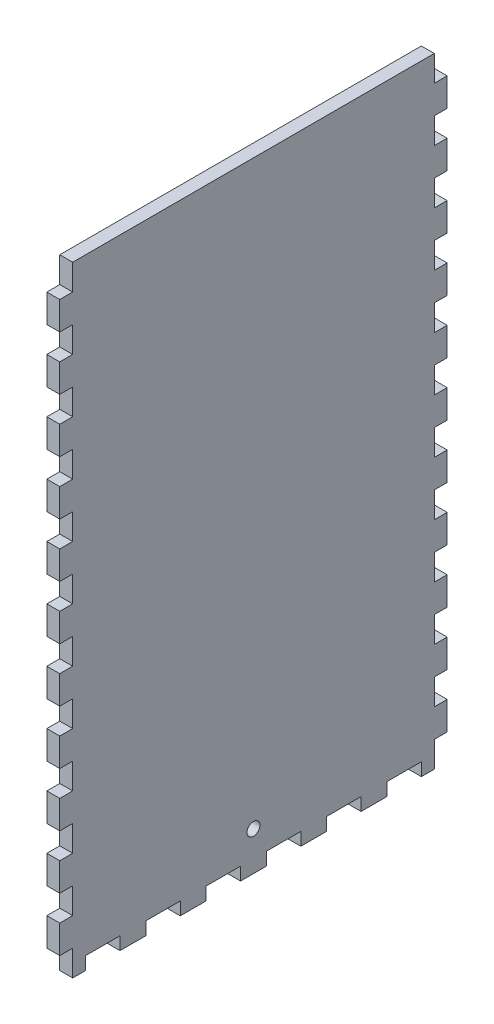
SolidWorks part; units mm, degrees
material "Acrylic (Medium-high impact)"
ref_plane "Front Plane" through (0, 0, 0) normal (0, 0, 1) x (1, 0, 0)
ref_plane "Top Plane" through (0, 0, 0) normal (0, 1, 0) x (1, 0, 0)
ref_plane "Right Plane" through (0, 0, 0) normal (1, 0, 0) x (0, 0, -1)
sketch "Sketch1" plane through (0, 0, 0) normal (0, 1, 0) x (1, 0, 0)
  line L1 (-254, 95.25) -> (254, 95.25)
  line L2 (-254, 95.25) -> (-254, -95.25)
  line L3 (-254, -95.25) -> (254, -95.25)
  line L4 (254, 95.25) -> (254, -95.25)
  point P4 (-254, 0)
  point P6 (0, 95.25)
  dimension "D1" = 190.5
  dimension "D2" = 508
extrude "Boss-Extrude1" add sketch "Sketch1" along normal blind 6.35
sketch "Sketch2" plane through (0, 6.35, 0) normal (0, 1, 0) x (1, 0, 0)
  line L0 (254, -95.25) -> (254, 95.25) construction
  line L1 (-254, 95.25) -> (254, 95.25)
  line L2 (-254, 95.25) -> (-254, -95.25)
  line L3 (-254, -95.25) -> (254, -95.25)
  line L4 (254, 95.25) -> (254, -95.25)
  line L5 (-254, -95.25) -> (254, -95.25) construction
  line L7 (-247.65, 88.9) -> (247.65, 88.9)
  line L8 (-247.65, 88.9) -> (-247.65, -88.9)
  line L9 (-247.65, -88.9) -> (247.65, -88.9)
  line L10 (247.65, 88.9) -> (247.65, -88.9)
  point P7 (-247.65, 0)
  point P14 (-254, 0)
  point P15 (0, -88.9)
  point P16 (0, -95.25)
  point P17 (247.65, 0)
  point P18 (254, 0)
  dimension "D1" = 6.35
  dimension "D2" = 6.35
extrude "Boss-Extrude2" add sketch "Sketch2" along normal blind 298.45
sketch "Sketch3" plane through (0, 0, 95.25) normal (0, 0, 1) x (1, 0, 0)
  line L0 (0, 304.8) -> (0, 0) construction
  line L1 (-254, 304.8) -> (254, 304.8) construction
  line L2 (-247.65, 6.35) -> (247.65, 6.35) construction
  line L4 (-3.302, 283.21) -> (-3.302, 6.35)
  line L5 (-3.302, 6.35) -> (3.302, 6.35)
  line L6 (3.302, 292.354) -> (3.302, 6.35)
  line L7 (3.302, 292.354) -> (-16.256, 292.354)
  line L9 (-5.842, 285.75) -> (-16.256, 285.75)
  line L10 (-16.256, 292.354) -> (-16.256, 285.75)
  line L11 (3.302, 101.6) -> (16.002, 101.6) construction
  line L12 (-254, 0) -> (254, 0) construction
  line L13 (12.827, 88.9) -> (12.827, 101.6) construction
  line L14 (9.652, 88.9) -> (16.002, 88.9)
  line L15 (9.652, 88.9) -> (9.652, 71.9667)
  line L16 (9.652, 71.9667) -> (16.002, 71.9667)
  line L17 (16.002, 88.9) -> (16.002, 71.9667)
  line L18 (9.652, 42.3333) -> (16.002, 42.3333)
  line L19 (9.652, 42.3333) -> (9.652, 59.2667)
  line L20 (9.652, 59.2667) -> (16.002, 59.2667)
  line L21 (16.002, 42.3333) -> (16.002, 59.2667)
  line L26 (9.652, 29.6333) -> (16.002, 29.6333)
  line L27 (9.652, 29.6333) -> (9.652, 12.7)
  line L28 (9.652, 12.7) -> (16.002, 12.7)
  line L29 (16.002, 29.6333) -> (16.002, 12.7)
  line L30 (12.827, 59.2667) -> (12.827, 71.9667) construction
  line L31 (12.827, 29.6333) -> (12.827, 42.3333) construction
  line L32 (12.827, 12.7) -> (12.827, 0) construction
  arc A0 (-3.302, 283.21) -> (-5.842, 285.75) centre (-5.842, 283.21) ccw
  point P5 (0, 6.35)
  dimension "D5" = 2.54
  dimension "D1" = 6.604
  dimension "D2" = 12.954
  dimension "D3" = 6.604
  dimension "D4" = 286.004
  dimension "D6" = 101.6
  dimension "D7" = 12.7
  dimension "D8" = 12.7
  dimension "D9" = 6.35
extrude "Cut-Extrude1" cut sketch "Sketch3" against normal blind 12.7
sketch "Sketch4" plane through (0, 0, -88.9) normal (0, 0, 1) x (1, 0, 0)
  line L0 (-254, 304.8) -> (254, 304.8) construction
  line L1 (-22.606, 304.8) -> (-16.256, 304.8)
  line L2 (-22.606, 304.8) -> (-22.606, 6.35)
  line L3 (-22.606, 6.35) -> (-16.256, 6.35)
  line L4 (-16.256, 304.8) -> (-16.256, 6.35)
  line L5 (6.477, 263.525) -> (6.477, 247.65) construction
  line L6 (-16.256, 292.354) -> (-16.256, 285.75) construction
  line L7 (3.302, 304.8) -> (9.652, 304.8)
  line L8 (3.302, 304.8) -> (3.302, 6.35)
  line L9 (3.302, 6.35) -> (9.652, 6.35)
  line L10 (9.652, 304.8) -> (9.652, 6.35)
  line L11 (247.65, 6.35) -> (-247.65, 6.35) construction
  line L12 (3.302, 6.35) -> (3.302, 292.354) construction
  line L13 (-16.256, 304.8) -> (-22.606, 304.8)
  line L14 (-16.256, 304.8) -> (-16.256, 292.1)
  line L15 (-16.256, 292.1) -> (-22.606, 292.1)
  line L16 (-22.606, 304.8) -> (-22.606, 292.1)
  line L17 (-16.256, 276.225) -> (-22.606, 276.225)
  line L18 (-16.256, 276.225) -> (-16.256, 263.525)
  line L19 (-16.256, 263.525) -> (-22.606, 263.525)
  line L20 (-22.606, 276.225) -> (-22.606, 263.525)
  line L21 (-22.606, 6.35) -> (-16.256, 6.35)
  line L22 (-22.606, 6.35) -> (-22.606, 19.05)
  line L23 (-22.606, 19.05) -> (-16.256, 19.05)
  line L24 (-16.256, 6.35) -> (-16.256, 19.05)
  line L25 (-22.606, 34.925) -> (-16.256, 34.925)
  line L26 (-22.606, 34.925) -> (-22.606, 47.625)
  line L27 (-22.606, 47.625) -> (-16.256, 47.625)
  line L28 (-16.256, 34.925) -> (-16.256, 47.625)
  line L29 (-22.606, 92.075) -> (-16.256, 92.075)
  line L30 (-22.606, 92.075) -> (-22.606, 104.775)
  line L31 (-22.606, 104.775) -> (-16.256, 104.775)
  line L32 (-16.256, 92.075) -> (-16.256, 104.775)
  line L33 (-22.606, 149.225) -> (-16.256, 149.225)
  line L34 (-22.606, 149.225) -> (-22.606, 161.925)
  line L35 (-22.606, 161.925) -> (-16.256, 161.925)
  line L36 (-16.256, 149.225) -> (-16.256, 161.925)
  line L37 (-22.606, 177.8) -> (-16.256, 177.8)
  line L38 (-22.606, 177.8) -> (-22.606, 190.5)
  line L39 (-22.606, 190.5) -> (-16.256, 190.5)
  line L40 (-16.256, 177.8) -> (-16.256, 190.5)
  line L41 (-22.606, 206.375) -> (-16.256, 206.375)
  line L42 (-22.606, 206.375) -> (-22.606, 219.075)
  line L43 (-22.606, 219.075) -> (-16.256, 219.075)
  line L44 (-16.256, 206.375) -> (-16.256, 219.075)
  line L45 (-22.606, 234.95) -> (-16.256, 234.95)
  line L46 (-22.606, 234.95) -> (-22.606, 247.65)
  line L47 (-22.606, 247.65) -> (-16.256, 247.65)
  line L48 (-16.256, 234.95) -> (-16.256, 247.65)
  line L49 (-16.256, 133.35) -> (-22.606, 133.35)
  line L50 (-16.256, 133.35) -> (-16.256, 120.65)
  line L51 (-16.256, 120.65) -> (-22.606, 120.65)
  line L52 (-22.606, 133.35) -> (-22.606, 120.65)
  line L53 (-16.256, 76.2) -> (-22.606, 76.2)
  line L54 (-16.256, 76.2) -> (-16.256, 63.5)
  line L55 (-16.256, 63.5) -> (-22.606, 63.5)
  line L56 (-22.606, 76.2) -> (-22.606, 63.5)
  line L57 (-19.431, 304.8) -> (-19.431, 292.1) construction
  line L58 (-19.431, 292.1) -> (-19.431, 276.225) construction
  line L59 (-19.431, 276.225) -> (-19.431, 263.525) construction
  line L60 (-19.431, 247.65) -> (-19.431, 234.95) construction
  line L61 (-19.431, 234.95) -> (-19.431, 219.075) construction
  line L62 (-19.431, 219.075) -> (-19.431, 206.375) construction
  line L63 (-19.431, 206.375) -> (-19.431, 190.5) construction
  line L64 (-19.431, 190.5) -> (-19.431, 177.8) construction
  line L65 (-19.431, 177.8) -> (-19.431, 161.925) construction
  line L66 (-19.431, 161.925) -> (-19.431, 149.225) construction
  line L67 (-19.431, 133.35) -> (-19.431, 120.65) construction
  line L68 (-19.431, 120.65) -> (-19.431, 104.775) construction
  line L69 (-19.431, 104.775) -> (-19.431, 92.075) construction
  line L70 (-19.431, 92.075) -> (-19.431, 76.2) construction
  line L71 (-19.431, 76.2) -> (-19.431, 63.5) construction
  line L72 (-19.431, 63.5) -> (-19.431, 47.625) construction
  line L73 (-19.431, 47.625) -> (-19.431, 34.925) construction
  line L74 (-19.431, 34.925) -> (-19.431, 19.05) construction
  line L75 (-19.431, 19.05) -> (-19.431, 6.35) construction
  line L76 (-19.431, 149.225) -> (-19.431, 133.35) construction
  line L77 (-19.431, 263.525) -> (-19.431, 247.65) construction
  line L78 (-6.477, 304.8) -> (-6.477, 0) construction
  line L79 (254, 304.8) -> (-254, 304.8) construction
  line L80 (254, 0) -> (-254, 0) construction
  line L81 (-6.477, 8.3493) -> (3.302, 8.3493) construction
  line L82 (-6.477, 8.3493) -> (-16.256, 8.3493) construction
  line L83 (6.477, 149.225) -> (6.477, 133.35) construction
  line L84 (6.477, 19.05) -> (6.477, 6.35) construction
  line L85 (6.477, 34.925) -> (6.477, 19.05) construction
  line L86 (6.477, 47.625) -> (6.477, 34.925) construction
  line L87 (6.477, 63.5) -> (6.477, 47.625) construction
  line L88 (6.477, 76.2) -> (6.477, 63.5) construction
  line L89 (6.477, 92.075) -> (6.477, 76.2) construction
  line L90 (6.477, 104.775) -> (6.477, 92.075) construction
  line L91 (6.477, 120.65) -> (6.477, 104.775) construction
  line L92 (6.477, 133.35) -> (6.477, 120.65) construction
  line L93 (6.477, 161.925) -> (6.477, 149.225) construction
  line L94 (6.477, 177.8) -> (6.477, 161.925) construction
  line L95 (6.477, 190.5) -> (6.477, 177.8) construction
  line L96 (6.477, 206.375) -> (6.477, 190.5) construction
  line L97 (6.477, 219.075) -> (6.477, 206.375) construction
  line L98 (6.477, 234.95) -> (6.477, 219.075) construction
  line L99 (6.477, 247.65) -> (6.477, 234.95) construction
  line L100 (6.477, 276.225) -> (6.477, 263.525) construction
  line L101 (6.477, 292.1) -> (6.477, 276.225) construction
  line L102 (6.477, 304.8) -> (6.477, 292.1) construction
  line L103 (9.652, 76.2) -> (9.652, 63.5)
  line L104 (3.302, 63.5) -> (9.652, 63.5)
  line L105 (3.302, 76.2) -> (3.302, 63.5)
  line L106 (3.302, 76.2) -> (9.652, 76.2)
  line L107 (9.652, 133.35) -> (9.652, 120.65)
  line L108 (3.302, 120.65) -> (9.652, 120.65)
  line L109 (3.302, 133.35) -> (3.302, 120.65)
  line L110 (3.302, 133.35) -> (9.652, 133.35)
  line L111 (3.302, 234.95) -> (3.302, 247.65)
  line L112 (9.652, 247.65) -> (3.302, 247.65)
  line L113 (9.652, 234.95) -> (9.652, 247.65)
  line L114 (9.652, 234.95) -> (3.302, 234.95)
  line L115 (3.302, 206.375) -> (3.302, 219.075)
  line L116 (9.652, 219.075) -> (3.302, 219.075)
  line L117 (9.652, 206.375) -> (9.652, 219.075)
  line L118 (9.652, 206.375) -> (3.302, 206.375)
  line L119 (3.302, 177.8) -> (3.302, 190.5)
  line L120 (9.652, 190.5) -> (3.302, 190.5)
  line L121 (9.652, 177.8) -> (9.652, 190.5)
  line L122 (9.652, 177.8) -> (3.302, 177.8)
  line L123 (3.302, 149.225) -> (3.302, 161.925)
  line L124 (9.652, 161.925) -> (3.302, 161.925)
  line L125 (9.652, 149.225) -> (9.652, 161.925)
  line L126 (9.652, 149.225) -> (3.302, 149.225)
  line L127 (3.302, 92.075) -> (3.302, 104.775)
  line L128 (9.652, 104.775) -> (3.302, 104.775)
  line L129 (9.652, 92.075) -> (9.652, 104.775)
  line L130 (9.652, 92.075) -> (3.302, 92.075)
  line L131 (3.302, 34.925) -> (3.302, 47.625)
  line L132 (9.652, 47.625) -> (3.302, 47.625)
  line L133 (9.652, 34.925) -> (9.652, 47.625)
  line L134 (9.652, 34.925) -> (3.302, 34.925)
  line L135 (3.302, 6.35) -> (3.302, 19.05)
  line L136 (9.652, 19.05) -> (3.302, 19.05)
  line L137 (9.652, 6.35) -> (9.652, 19.05)
  line L138 (9.652, 6.35) -> (3.302, 6.35)
  line L139 (9.652, 276.225) -> (9.652, 263.525)
  line L140 (3.302, 263.525) -> (9.652, 263.525)
  line L141 (3.302, 276.225) -> (3.302, 263.525)
  line L142 (3.302, 276.225) -> (9.652, 276.225)
  line L143 (9.652, 304.8) -> (9.652, 292.1)
  line L144 (3.302, 292.1) -> (9.652, 292.1)
  line L145 (3.302, 304.8) -> (3.302, 292.1)
  line L146 (3.302, 304.8) -> (9.652, 304.8)
  line L147 (3.302, 304.8) -> (3.302, 6.35)
  line L148 (9.652, 6.35) -> (3.302, 6.35)
  line L149 (9.652, 304.8) -> (9.652, 6.35)
  line L150 (9.652, 304.8) -> (3.302, 304.8)
  point P14 (-16.256, 289.052)
  dimension "D1" = 6.35
  dimension "D2" = 12.7
extrude "Cut-Extrude2" cut sketch "Sketch4" against normal up to next (6.35 mm away) contours L17 L4 L15 L2 | L2 L47 L4 L19 | L45 L2 L43 L4 | L41 L2 L39 L4 | L37 L2 L35 L4 | L49 L4 L33 L2 | L4 L51 L2 L31 | L53 L4 L29 L2 | L4 L55 L2 L27 | L25 L2 L23 L4
ref_plane "Plane1" through (-6.477, 0, 0) normal (-1, 0, 0) x (0, 0, 1)
mirror "Mirror1" about plane through (-6.477, 0, 0) normal (-1, 0, 0) of "Cut-Extrude2"
sketch "Sketch5" plane through (0, 0, 0) normal (0, -1, 0) x (-1, 0, 0)
  line L0 (-227.9316, -95.25) -> (-227.9316, -88.9)
  line L1 (-247.65, 88.9) -> (247.65, 88.9)
  line L2 (-247.65, 88.9) -> (-247.65, -88.9)
  line L3 (-247.65, -88.9) -> (247.65, -88.9)
  line L4 (247.65, 88.9) -> (247.65, -88.9)
  line L5 (-254, -95.25) -> (-241.3, -95.25)
  line L6 (-254, -95.25) -> (-254, -88.9)
  line L7 (-254, -88.9) -> (-241.3, -88.9)
  line L8 (-241.3, -95.25) -> (-241.3, -88.9)
  line L9 (-227.9316, -95.25) -> (-215.2316, -95.25)
  line L10 (-227.9316, -88.9) -> (-215.2316, -88.9)
  line L11 (-215.2316, -95.25) -> (-215.2316, -88.9)
  line L12 (-201.8632, -95.25) -> (-201.8632, -88.9)
  line L13 (-201.8632, -95.25) -> (-189.1632, -95.25)
  line L14 (-201.8632, -88.9) -> (-189.1632, -88.9)
  line L15 (-189.1632, -95.25) -> (-189.1632, -88.9)
  line L16 (-175.7947, -95.25) -> (-175.7947, -88.9)
  line L17 (-175.7947, -95.25) -> (-163.0947, -95.25)
  line L18 (-175.7947, -88.9) -> (-163.0947, -88.9)
  line L19 (-163.0947, -95.25) -> (-163.0947, -88.9)
  line L20 (-149.7263, -95.25) -> (-149.7263, -88.9)
  line L21 (-149.7263, -95.25) -> (-137.0263, -95.25)
  line L22 (-149.7263, -88.9) -> (-137.0263, -88.9)
  line L23 (-137.0263, -95.25) -> (-137.0263, -88.9)
  line L24 (-123.6579, -95.25) -> (-123.6579, -88.9)
  line L25 (-123.6579, -95.25) -> (-110.9579, -95.25)
  line L26 (-123.6579, -88.9) -> (-110.9579, -88.9)
  line L27 (-110.9579, -95.25) -> (-110.9579, -88.9)
  line L28 (-97.5895, -95.25) -> (-97.5895, -88.9)
  line L29 (-97.5895, -95.25) -> (-84.8895, -95.25)
  line L30 (-97.5895, -88.9) -> (-84.8895, -88.9)
  line L31 (-84.8895, -95.25) -> (-84.8895, -88.9)
  line L32 (-71.5211, -95.25) -> (-71.5211, -88.9)
  line L33 (-71.5211, -95.25) -> (-58.8211, -95.25)
  line L34 (-71.5211, -88.9) -> (-58.8211, -88.9)
  line L35 (-58.8211, -95.25) -> (-58.8211, -88.9)
  line L36 (-45.4526, -95.25) -> (-45.4526, -88.9)
  line L37 (-45.4526, -95.25) -> (-32.7526, -95.25)
  line L38 (-45.4526, -88.9) -> (-32.7526, -88.9)
  line L39 (-32.7526, -95.25) -> (-32.7526, -88.9)
  line L40 (-19.3842, -95.25) -> (-19.3842, -88.9)
  line L41 (-19.3842, -95.25) -> (-6.6842, -95.25)
  line L42 (-19.3842, -88.9) -> (-6.6842, -88.9)
  line L43 (-6.6842, -95.25) -> (-6.6842, -88.9)
  line L44 (6.6842, -95.25) -> (6.6842, -88.9)
  line L45 (6.6842, -95.25) -> (19.3842, -95.25)
  line L46 (6.6842, -88.9) -> (19.3842, -88.9)
  line L47 (19.3842, -95.25) -> (19.3842, -88.9)
  line L48 (32.7526, -95.25) -> (32.7526, -88.9)
  line L49 (32.7526, -95.25) -> (45.4526, -95.25)
  line L50 (32.7526, -88.9) -> (45.4526, -88.9)
  line L51 (45.4526, -95.25) -> (45.4526, -88.9)
  line L52 (58.8211, -95.25) -> (58.8211, -88.9)
  line L53 (58.8211, -95.25) -> (71.5211, -95.25)
  line L54 (58.8211, -88.9) -> (71.5211, -88.9)
  line L55 (71.5211, -95.25) -> (71.5211, -88.9)
  line L56 (84.8895, -95.25) -> (84.8895, -88.9)
  line L57 (84.8895, -95.25) -> (97.5895, -95.25)
  line L58 (84.8895, -88.9) -> (97.5895, -88.9)
  line L59 (97.5895, -95.25) -> (97.5895, -88.9)
  line L60 (110.9579, -95.25) -> (110.9579, -88.9)
  line L61 (110.9579, -95.25) -> (123.6579, -95.25)
  line L62 (110.9579, -88.9) -> (123.6579, -88.9)
  line L63 (123.6579, -95.25) -> (123.6579, -88.9)
  line L64 (137.0263, -95.25) -> (137.0263, -88.9)
  line L65 (137.0263, -95.25) -> (149.7263, -95.25)
  line L66 (137.0263, -88.9) -> (149.7263, -88.9)
  line L67 (149.7263, -95.25) -> (149.7263, -88.9)
  line L68 (163.0947, -95.25) -> (163.0947, -88.9)
  line L69 (163.0947, -95.25) -> (175.7947, -95.25)
  line L70 (163.0947, -88.9) -> (175.7947, -88.9)
  line L71 (175.7947, -95.25) -> (175.7947, -88.9)
  line L72 (189.1632, -95.25) -> (189.1632, -88.9)
  line L73 (189.1632, -95.25) -> (201.8632, -95.25)
  line L74 (189.1632, -88.9) -> (201.8632, -88.9)
  line L75 (201.8632, -95.25) -> (201.8632, -88.9)
  line L76 (215.2316, -95.25) -> (215.2316, -88.9)
  line L77 (215.2316, -95.25) -> (227.9316, -95.25)
  line L78 (215.2316, -88.9) -> (227.9316, -88.9)
  line L79 (227.9316, -95.25) -> (227.9316, -88.9)
  line L80 (241.3, -95.25) -> (241.3, -88.9)
  line L81 (241.3, -95.25) -> (254, -95.25)
  line L82 (241.3, -88.9) -> (254, -88.9)
  line L83 (254, -95.25) -> (254, -88.9)
  line L84 (-167.64, 0) -> (167.64, 0) construction
  line L85 (254, 95.25) -> (254, 88.9)
  line L86 (241.3, 88.9) -> (254, 88.9)
  line L87 (241.3, 95.25) -> (254, 95.25)
  line L88 (241.3, 95.25) -> (241.3, 88.9)
  line L89 (227.9316, 95.25) -> (227.9316, 88.9)
  line L90 (215.2316, 88.9) -> (227.9316, 88.9)
  line L91 (215.2316, 95.25) -> (227.9316, 95.25)
  line L92 (215.2316, 95.25) -> (215.2316, 88.9)
  line L93 (201.8632, 95.25) -> (201.8632, 88.9)
  line L94 (189.1632, 88.9) -> (201.8632, 88.9)
  line L95 (189.1632, 95.25) -> (201.8632, 95.25)
  line L96 (189.1632, 95.25) -> (189.1632, 88.9)
  line L97 (175.7947, 95.25) -> (175.7947, 88.9)
  line L98 (163.0947, 88.9) -> (175.7947, 88.9)
  line L99 (163.0947, 95.25) -> (175.7947, 95.25)
  line L100 (163.0947, 95.25) -> (163.0947, 88.9)
  line L101 (149.7263, 95.25) -> (149.7263, 88.9)
  line L102 (137.0263, 88.9) -> (149.7263, 88.9)
  line L103 (137.0263, 95.25) -> (149.7263, 95.25)
  line L104 (137.0263, 95.25) -> (137.0263, 88.9)
  line L105 (123.6579, 95.25) -> (123.6579, 88.9)
  line L106 (110.9579, 88.9) -> (123.6579, 88.9)
  line L107 (110.9579, 95.25) -> (123.6579, 95.25)
  line L108 (110.9579, 95.25) -> (110.9579, 88.9)
  line L109 (97.5895, 95.25) -> (97.5895, 88.9)
  line L110 (84.8895, 88.9) -> (97.5895, 88.9)
  line L111 (84.8895, 95.25) -> (97.5895, 95.25)
  line L112 (84.8895, 95.25) -> (84.8895, 88.9)
  line L113 (71.5211, 95.25) -> (71.5211, 88.9)
  line L114 (58.8211, 88.9) -> (71.5211, 88.9)
  line L115 (58.8211, 95.25) -> (71.5211, 95.25)
  line L116 (58.8211, 95.25) -> (58.8211, 88.9)
  line L117 (45.4526, 95.25) -> (45.4526, 88.9)
  line L118 (32.7526, 88.9) -> (45.4526, 88.9)
  line L119 (32.7526, 95.25) -> (45.4526, 95.25)
  line L120 (32.7526, 95.25) -> (32.7526, 88.9)
  line L121 (19.3842, 95.25) -> (19.3842, 88.9)
  line L122 (6.6842, 88.9) -> (19.3842, 88.9)
  line L123 (6.6842, 95.25) -> (19.3842, 95.25)
  line L124 (6.6842, 95.25) -> (6.6842, 88.9)
  line L125 (-6.6842, 95.25) -> (-6.6842, 88.9)
  line L126 (-19.3842, 88.9) -> (-6.6842, 88.9)
  line L127 (-19.3842, 95.25) -> (-6.6842, 95.25)
  line L128 (-19.3842, 95.25) -> (-19.3842, 88.9)
  line L129 (-32.7526, 95.25) -> (-32.7526, 88.9)
  line L130 (-45.4526, 88.9) -> (-32.7526, 88.9)
  line L131 (-45.4526, 95.25) -> (-32.7526, 95.25)
  line L132 (-45.4526, 95.25) -> (-45.4526, 88.9)
  line L133 (-58.8211, 95.25) -> (-58.8211, 88.9)
  line L134 (-71.5211, 88.9) -> (-58.8211, 88.9)
  line L135 (-71.5211, 95.25) -> (-58.8211, 95.25)
  line L136 (-71.5211, 95.25) -> (-71.5211, 88.9)
  line L137 (-84.8895, 95.25) -> (-84.8895, 88.9)
  line L138 (-97.5895, 88.9) -> (-84.8895, 88.9)
  line L139 (-97.5895, 95.25) -> (-84.8895, 95.25)
  line L140 (-97.5895, 95.25) -> (-97.5895, 88.9)
  line L141 (-110.9579, 95.25) -> (-110.9579, 88.9)
  line L142 (-123.6579, 88.9) -> (-110.9579, 88.9)
  line L143 (-123.6579, 95.25) -> (-110.9579, 95.25)
  line L144 (-123.6579, 95.25) -> (-123.6579, 88.9)
  line L145 (-137.0263, 95.25) -> (-137.0263, 88.9)
  line L146 (-149.7263, 88.9) -> (-137.0263, 88.9)
  line L147 (-149.7263, 95.25) -> (-137.0263, 95.25)
  line L148 (-149.7263, 95.25) -> (-149.7263, 88.9)
  line L149 (-163.0947, 95.25) -> (-163.0947, 88.9)
  line L150 (-175.7947, 88.9) -> (-163.0947, 88.9)
  line L151 (-175.7947, 95.25) -> (-163.0947, 95.25)
  line L152 (-175.7947, 95.25) -> (-175.7947, 88.9)
  line L153 (-189.1632, 95.25) -> (-189.1632, 88.9)
  line L154 (-201.8632, 88.9) -> (-189.1632, 88.9)
  line L155 (-201.8632, 95.25) -> (-189.1632, 95.25)
  line L156 (-201.8632, 95.25) -> (-201.8632, 88.9)
  line L157 (-215.2316, 95.25) -> (-215.2316, 88.9)
  line L158 (-227.9316, 88.9) -> (-215.2316, 88.9)
  line L159 (-227.9316, 95.25) -> (-215.2316, 95.25)
  line L160 (-241.3, 95.25) -> (-241.3, 88.9)
  line L161 (-254, 88.9) -> (-241.3, 88.9)
  line L162 (-254, 95.25) -> (-254, 88.9)
  line L163 (-254, 95.25) -> (-241.3, 95.25)
  line L164 (-247.65, 88.9) -> (247.65, 88.9)
  line L165 (-227.9316, 95.25) -> (-227.9316, 88.9)
  line L166 (-254, 65.6167) -> (-254, 52.9167)
  line L167 (-254, 95.25) -> (-247.65, 95.25)
  line L168 (-254, 95.25) -> (-254, 82.55)
  line L169 (-254, 82.55) -> (-247.65, 82.55)
  line L170 (-247.65, 95.25) -> (-247.65, 82.55)
  line L171 (-254, 65.6167) -> (-247.65, 65.6167)
  line L172 (-247.65, 65.6167) -> (-247.65, 52.9167)
  line L173 (-254, 52.9167) -> (-247.65, 52.9167)
  line L174 (-254, 35.9833) -> (-254, 23.2833)
  line L175 (-254, 35.9833) -> (-247.65, 35.9833)
  line L176 (-247.65, 35.9833) -> (-247.65, 23.2833)
  line L177 (-254, 23.2833) -> (-247.65, 23.2833)
  line L178 (-254, 6.35) -> (-254, -6.35)
  line L179 (-254, 6.35) -> (-247.65, 6.35)
  line L180 (-247.65, 6.35) -> (-247.65, -6.35)
  line L181 (-254, -6.35) -> (-247.65, -6.35)
  line L182 (-254, -23.2833) -> (-254, -35.9833)
  line L183 (-254, -23.2833) -> (-247.65, -23.2833)
  line L184 (-247.65, -23.2833) -> (-247.65, -35.9833)
  line L185 (-254, -35.9833) -> (-247.65, -35.9833)
  line L186 (-254, -52.9167) -> (-254, -65.6167)
  line L187 (-254, -52.9167) -> (-247.65, -52.9167)
  line L188 (-247.65, -52.9167) -> (-247.65, -65.6167)
  line L189 (-254, -65.6167) -> (-247.65, -65.6167)
  line L190 (-254, -82.55) -> (-254, -95.25)
  line L191 (-254, -82.55) -> (-247.65, -82.55)
  line L192 (-247.65, -82.55) -> (-247.65, -95.25)
  line L193 (-254, -95.25) -> (-247.65, -95.25)
  line L194 (0, 104.775) -> (0, -104.775) construction
  line L195 (254, -95.25) -> (247.65, -95.25)
  line L196 (247.65, -82.55) -> (247.65, -95.25)
  line L197 (254, -82.55) -> (247.65, -82.55)
  line L198 (254, -82.55) -> (254, -95.25)
  line L199 (254, -65.6167) -> (247.65, -65.6167)
  line L200 (247.65, -52.9167) -> (247.65, -65.6167)
  line L201 (254, -52.9167) -> (247.65, -52.9167)
  line L202 (254, -52.9167) -> (254, -65.6167)
  line L203 (254, -35.9833) -> (247.65, -35.9833)
  line L204 (247.65, -23.2833) -> (247.65, -35.9833)
  line L205 (254, -23.2833) -> (247.65, -23.2833)
  line L206 (254, -23.2833) -> (254, -35.9833)
  line L207 (254, -6.35) -> (247.65, -6.35)
  line L208 (247.65, 6.35) -> (247.65, -6.35)
  line L209 (254, 6.35) -> (247.65, 6.35)
  line L210 (254, 6.35) -> (254, -6.35)
  line L211 (254, 23.2833) -> (247.65, 23.2833)
  line L212 (247.65, 35.9833) -> (247.65, 23.2833)
  line L213 (254, 35.9833) -> (247.65, 35.9833)
  line L214 (254, 35.9833) -> (254, 23.2833)
  line L215 (254, 52.9167) -> (247.65, 52.9167)
  line L216 (247.65, 65.6167) -> (247.65, 52.9167)
  line L217 (254, 65.6167) -> (247.65, 65.6167)
  line L218 (247.65, 95.25) -> (247.65, 82.55)
  line L219 (254, 82.55) -> (247.65, 82.55)
  line L220 (254, 95.25) -> (254, 82.55)
  line L221 (254, 95.25) -> (247.65, 95.25)
  line L222 (254, 65.6167) -> (254, 52.9167)
  line L223 (254, 95.25) -> (254, 88.9)
  line L224 (254, -95.25) -> (254, -88.9)
  line L225 (247.65, 88.9) -> (247.65, -88.9)
  line M114 (254, -95.25) -> (254, 95.25)
  dimension "D1" = 12.7
  dimension "D3" = 6.35
  dimension "D5" = 12.7
  dimension "D2" = 20
  dimension "D4" = 7
sketch "Sketch6" plane through (0, 0, 0) normal (0, 1, 0) x (1, 0, 0)
  line L1 (-247.65, 117.4399) -> (267.1511, 117.4399)
  line L2 (-247.65, 117.4399) -> (-247.65, -137.4416)
  line L3 (-247.65, -137.4416) -> (267.1511, -137.4416)
  line L4 (267.1511, 117.4399) -> (267.1511, -137.4416)
  line L6 (-247.65, 88.9) -> (-247.65, -88.9) construction
extrude "Cut-Extrude5" cut sketch "Sketch6" along normal through all
extrude "Cut-Extrude6" cut sketch "Sketch5" against normal blind 6.35 contours L199 L4 L197 M114 | L203 L4 L201 M114 | L207 L4 L205 M114 | L211 L4 L209 M114 | L215 L4 L213 M114 | L219 L4 L217 M114
sketch "Sketch7" plane through (-254, 0, 0) normal (-1, 0, 0) x (0, 0, 1)
  line L0 (-95.25, 26.5545) -> (-95.25, 39.2545)
  line L1 (-95.25, 0) -> (-88.9, 0)
  line L2 (-95.25, 0) -> (-95.25, 12.7)
  line L3 (-95.25, 12.7) -> (-88.9, 12.7)
  line L4 (-88.9, 0) -> (-88.9, 12.7)
  line L5 (-95.25, 39.2545) -> (-88.9, 39.2545)
  line L6 (-88.9, 26.5545) -> (-88.9, 39.2545)
  line L7 (-95.25, 26.5545) -> (-88.9, 26.5545)
  line L8 (-95.25, 53.1091) -> (-95.25, 65.8091)
  line L9 (-95.25, 65.8091) -> (-88.9, 65.8091)
  line L10 (-88.9, 53.1091) -> (-88.9, 65.8091)
  line L11 (-95.25, 53.1091) -> (-88.9, 53.1091)
  line L12 (-95.25, 79.6636) -> (-95.25, 92.3636)
  line L13 (-95.25, 92.3636) -> (-88.9, 92.3636)
  line L14 (-88.9, 79.6636) -> (-88.9, 92.3636)
  line L15 (-95.25, 79.6636) -> (-88.9, 79.6636)
  line L16 (-95.25, 106.2182) -> (-95.25, 118.9182)
  line L17 (-95.25, 118.9182) -> (-88.9, 118.9182)
  line L18 (-88.9, 106.2182) -> (-88.9, 118.9182)
  line L19 (-95.25, 106.2182) -> (-88.9, 106.2182)
  line L20 (-95.25, 132.7727) -> (-95.25, 145.4727)
  line L21 (-95.25, 145.4727) -> (-88.9, 145.4727)
  line L22 (-88.9, 132.7727) -> (-88.9, 145.4727)
  line L23 (-95.25, 132.7727) -> (-88.9, 132.7727)
  line L24 (-95.25, 159.3273) -> (-95.25, 172.0273)
  line L25 (-95.25, 172.0273) -> (-88.9, 172.0273)
  line L26 (-88.9, 159.3273) -> (-88.9, 172.0273)
  line L27 (-95.25, 159.3273) -> (-88.9, 159.3273)
  line L28 (-95.25, 185.8818) -> (-95.25, 198.5818)
  line L29 (-95.25, 198.5818) -> (-88.9, 198.5818)
  line L30 (-88.9, 185.8818) -> (-88.9, 198.5818)
  line L31 (-95.25, 185.8818) -> (-88.9, 185.8818)
  line L32 (-95.25, 212.4364) -> (-95.25, 225.1364)
  line L33 (-95.25, 225.1364) -> (-88.9, 225.1364)
  line L34 (-88.9, 212.4364) -> (-88.9, 225.1364)
  line L35 (-95.25, 212.4364) -> (-88.9, 212.4364)
  line L36 (-95.25, 238.9909) -> (-95.25, 251.6909)
  line L37 (-95.25, 251.6909) -> (-88.9, 251.6909)
  line L38 (-88.9, 238.9909) -> (-88.9, 251.6909)
  line L39 (-95.25, 238.9909) -> (-88.9, 238.9909)
  line L40 (-95.25, 265.5455) -> (-95.25, 278.2455)
  line L41 (-95.25, 278.2455) -> (-88.9, 278.2455)
  line L42 (-88.9, 265.5455) -> (-88.9, 278.2455)
  line L43 (-95.25, 265.5455) -> (-88.9, 265.5455)
  line L44 (-95.25, 292.1) -> (-95.25, 304.8)
  line L45 (-95.25, 304.8) -> (-88.9, 304.8)
  line L46 (-88.9, 292.1) -> (-88.9, 304.8)
  line L47 (-95.25, 292.1) -> (-88.9, 292.1)
  line L48 (0, -3.4925) -> (0, 3.4925) construction
  line L49 (95.25, 292.1) -> (88.9, 292.1)
  line L50 (88.9, 292.1) -> (88.9, 304.8)
  line L51 (95.25, 304.8) -> (88.9, 304.8)
  line L52 (95.25, 292.1) -> (95.25, 304.8)
  line L53 (95.25, 265.5455) -> (88.9, 265.5455)
  line L54 (88.9, 265.5455) -> (88.9, 278.2455)
  line L55 (95.25, 278.2455) -> (88.9, 278.2455)
  line L56 (95.25, 265.5455) -> (95.25, 278.2455)
  line L57 (95.25, 238.9909) -> (88.9, 238.9909)
  line L58 (88.9, 238.9909) -> (88.9, 251.6909)
  line L59 (95.25, 251.6909) -> (88.9, 251.6909)
  line L60 (95.25, 238.9909) -> (95.25, 251.6909)
  line L61 (95.25, 212.4364) -> (88.9, 212.4364)
  line L62 (88.9, 212.4364) -> (88.9, 225.1364)
  line L63 (95.25, 225.1364) -> (88.9, 225.1364)
  line L64 (95.25, 212.4364) -> (95.25, 225.1364)
  line L65 (95.25, 185.8818) -> (88.9, 185.8818)
  line L66 (88.9, 185.8818) -> (88.9, 198.5818)
  line L67 (95.25, 198.5818) -> (88.9, 198.5818)
  line L68 (95.25, 185.8818) -> (95.25, 198.5818)
  line L69 (95.25, 159.3273) -> (88.9, 159.3273)
  line L70 (88.9, 159.3273) -> (88.9, 172.0273)
  line L71 (95.25, 172.0273) -> (88.9, 172.0273)
  line L72 (95.25, 159.3273) -> (95.25, 172.0273)
  line L73 (95.25, 132.7727) -> (88.9, 132.7727)
  line L74 (88.9, 132.7727) -> (88.9, 145.4727)
  line L75 (95.25, 145.4727) -> (88.9, 145.4727)
  line L76 (95.25, 132.7727) -> (95.25, 145.4727)
  line L77 (95.25, 106.2182) -> (88.9, 106.2182)
  line L78 (88.9, 106.2182) -> (88.9, 118.9182)
  line L79 (95.25, 118.9182) -> (88.9, 118.9182)
  line L80 (95.25, 106.2182) -> (95.25, 118.9182)
  line L81 (95.25, 79.6636) -> (88.9, 79.6636)
  line L82 (88.9, 79.6636) -> (88.9, 92.3636)
  line L83 (95.25, 92.3636) -> (88.9, 92.3636)
  line L84 (95.25, 79.6636) -> (95.25, 92.3636)
  line L85 (95.25, 53.1091) -> (88.9, 53.1091)
  line L86 (88.9, 53.1091) -> (88.9, 65.8091)
  line L87 (95.25, 65.8091) -> (88.9, 65.8091)
  line L88 (95.25, 53.1091) -> (95.25, 65.8091)
  line L89 (95.25, 26.5545) -> (88.9, 26.5545)
  line L90 (88.9, 26.5545) -> (88.9, 39.2545)
  line L91 (95.25, 39.2545) -> (88.9, 39.2545)
  line L92 (88.9, 0) -> (88.9, 12.7)
  line L93 (95.25, 12.7) -> (88.9, 12.7)
  line L94 (95.25, 0) -> (95.25, 12.7)
  line L95 (95.25, 0) -> (88.9, 0)
  line L96 (95.25, 26.5545) -> (95.25, 39.2545)
  dimension "D1" = 12.7
  dimension "D2" = 6.35
  dimension "D3" = 12
extrude "Cut-Extrude7" cut sketch "Sketch7" against normal through all
sketch "Sketch8" plane through (-254, 0, 0) normal (-1, 0, 0) x (0, 0, 1)
  line L1 (-6.35, 0) -> (6.35, 0) construction
  circle A0 centre (0, 19.05) radius 3.175
  point P2 (0, 0)
  dimension "D1" = 6.35
  dimension "D2" = 19.05
extrude "Cut-Extrude8" cut sketch "Sketch8" against normal through all
